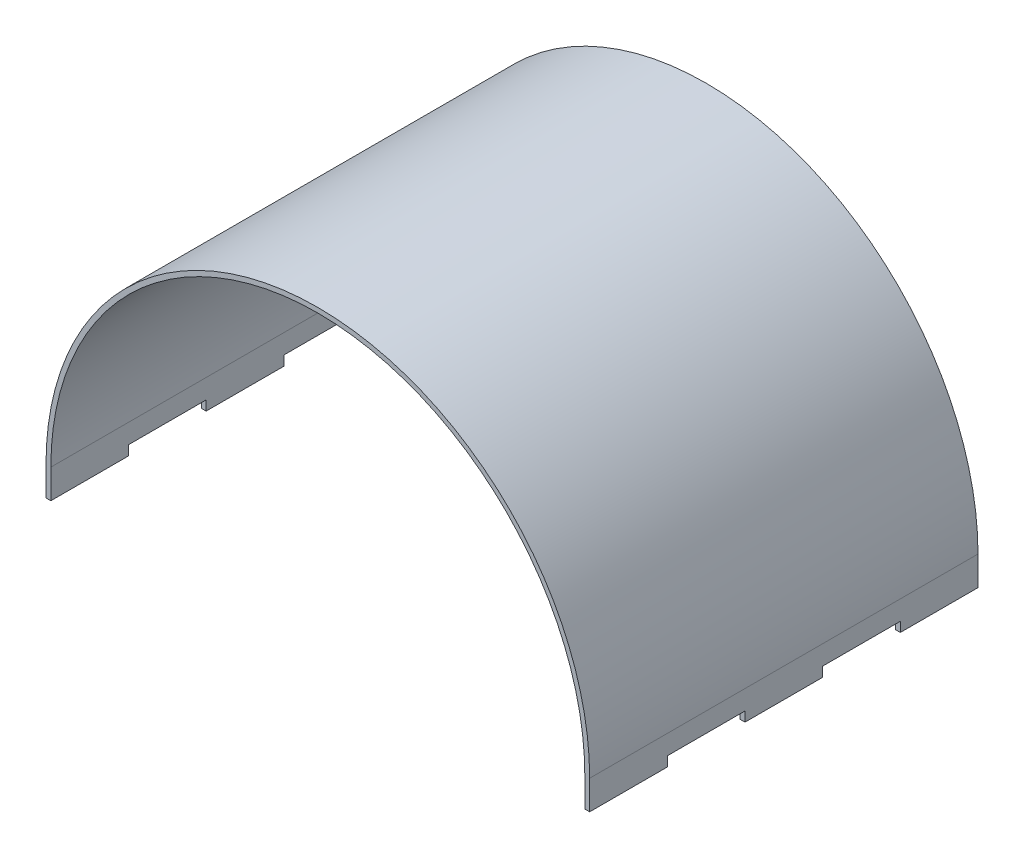
SolidWorks part; units mm, degrees
ref_plane "Front Plane" through (0, 0, 0) normal (0, 0, 1) x (1, 0, 0)
ref_plane "Top Plane" through (0, 0, 0) normal (0, 1, 0) x (1, 0, 0)
ref_plane "Right Plane" through (0, 0, 0) normal (1, 0, 0) x (0, 0, -1)
sketch "Sketch1" plane through (0, 0, 0) normal (0, 0, 1) x (1, 0, 0)
  line L0 (0, 0) -> (3.175, 0)
  line L1 (352.425, 0) -> (355.6, 0)
  line L2 (0, 0) -> (0, 19.05)
  line L3 (3.175, 0) -> (3.175, 19.05)
  line L4 (352.425, 0) -> (352.425, 19.05)
  line L5 (355.6, 0) -> (355.6, 19.05)
  arc A0 (0, 19.05) -> (355.6, 19.05) centre (177.8, 19.05) cw
  arc A1 (352.425, 19.05) -> (3.175, 19.05) centre (177.8, 19.05) ccw
  dimension "D1" = 3.175
  dimension "D2" = 3.175
  dimension "D3" = 355.6
  dimension "D4" = 19.05
  dimension "D5" = 19.05
  dimension "D6" = 19.05
  dimension "D7" = 19.05
extrude "Boss-Extrude1" add sketch "Sketch1" along normal blind 254
sketch "Sketch2" plane through (355.6, 0, 0) normal (1, 0, 0) x (0, 0, -1)
  line L0 (-254, 0) -> (0, 0) construction
  line L1 (-203.2, 0) -> (-152.4, 0)
  line L2 (-203.2, 0) -> (-203.2, 6.35)
  line L3 (-203.2, 6.35) -> (-152.4, 6.35)
  line L4 (-152.4, 0) -> (-152.4, 6.35)
  line L5 (-254, 0) -> (-254, 19.05) construction
  line L6 (-101.6, 0) -> (-50.8, 0)
  line L7 (-101.6, 0) -> (-101.6, 6.35)
  line L8 (-101.6, 6.35) -> (-50.8, 6.35)
  line L9 (-50.8, 0) -> (-50.8, 6.35)
  dimension "D1" = 50.8
  dimension "D2" = 6.35
  dimension "D3" = 50.8
  dimension "D4" = 6.35
  dimension "D5" = 50.8
  dimension "D6" = 50.8
extrude "Cut-Extrude1" cut sketch "Sketch2" against normal through all contours L2 L1 L4 L3 | L7 L6 L9 L8
